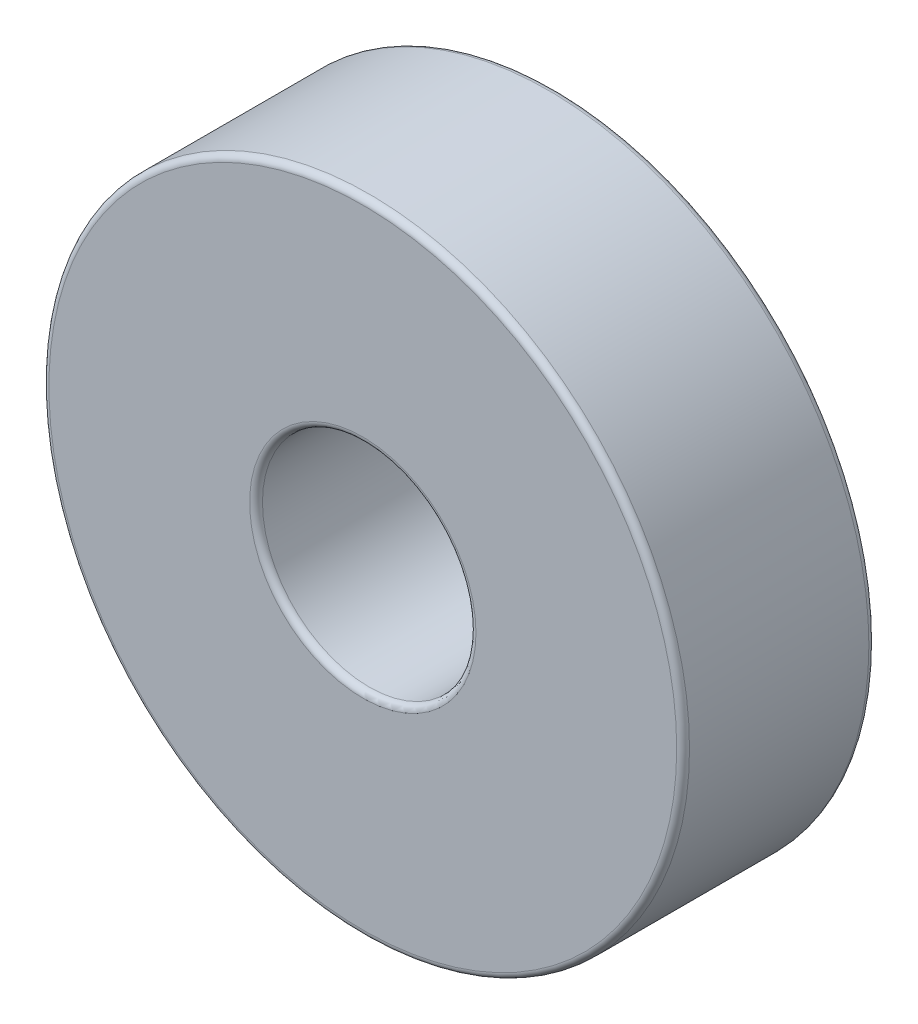
SolidWorks part; units mm, degrees
ref_plane "前基準面" through (0, 0, 0) normal (0, 0, 1) x (1, 0, 0)
ref_plane "上基準面" through (0, 0, 0) normal (0, 1, 0) x (1, 0, 0)
ref_plane "右基準面" through (0, 0, 0) normal (1, 0, 0) x (0, 0, -1)
sketch "草圖1" plane through (0, 0, 0) normal (0, 0, 1) x (1, 0, 0)
  circle A0 centre (0, 0) radius 5
  circle A1 centre (0, 0) radius 15
  dimension "D1" = 10
  dimension "D2" = 30
extrude "伸長1" add sketch "草圖1" along normal blind 9
fillet "圓角1" radius 0.3 4 edges at (5, 0, 9) (5, 0, 0) (15, 0, 9) (15, 0, 0)
